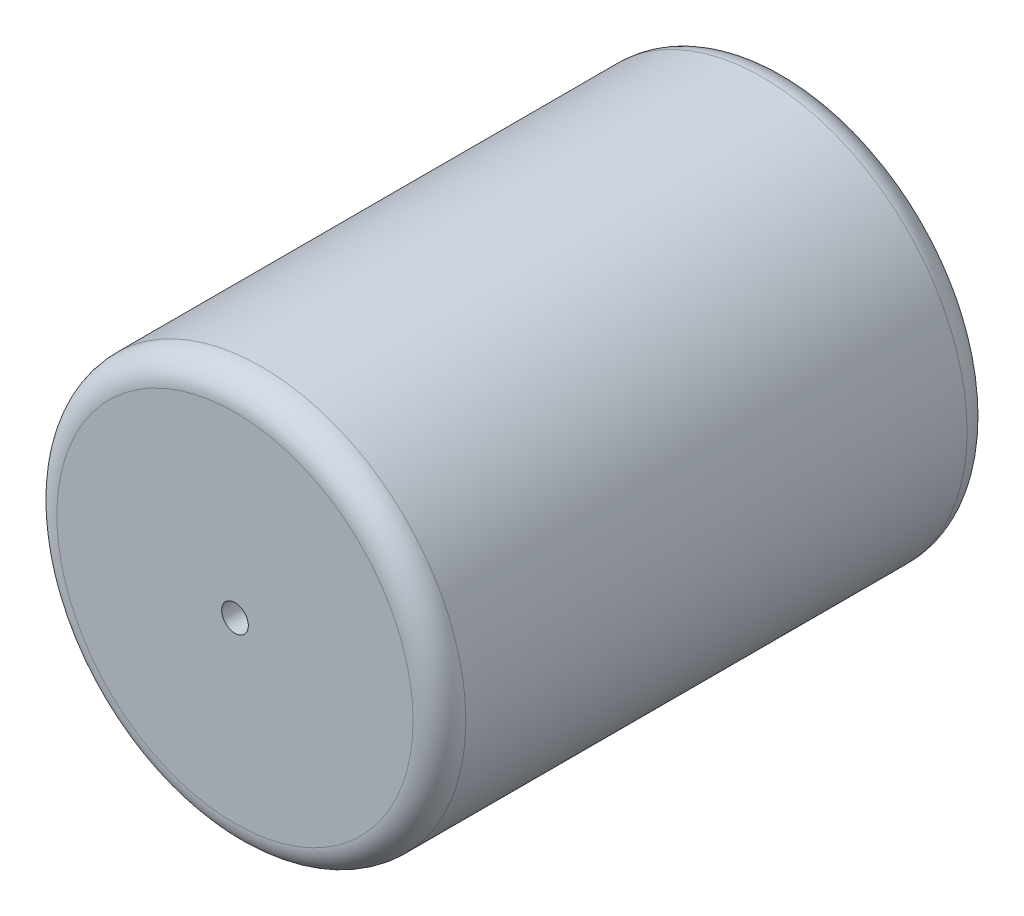
SolidWorks part; units mm, degrees
ref_plane "Front Plane" through (0, 0, 0) normal (0, 0, 1) x (1, 0, 0)
ref_plane "Top Plane" through (0, 0, 0) normal (0, 1, 0) x (1, 0, 0)
ref_plane "Right Plane" through (0, 0, 0) normal (1, 0, 0) x (0, 0, -1)
sketch "Sketch1" plane through (0, 0, 0) normal (0, 0, 1) x (1, 0, 0)
  circle A0 centre (0, 0) radius 7.75
  dimension "D1" = 15.5
extrude "Boss-Extrude1" add sketch "Sketch1" along normal blind 21
fillet "Fillet1" radius 1 2 edges at (7.75, 0, 21) (7.75, 0, 0)
sketch "Sketch2" plane through (0, 0, 21) normal (0, 0, 1) x (1, 0, 0)
  circle A0 centre (0, 0) radius 0.505
  dimension "D1" = 1.01
extrude "Cut-Extrude1" cut sketch "Sketch2" against normal blind 51.7
